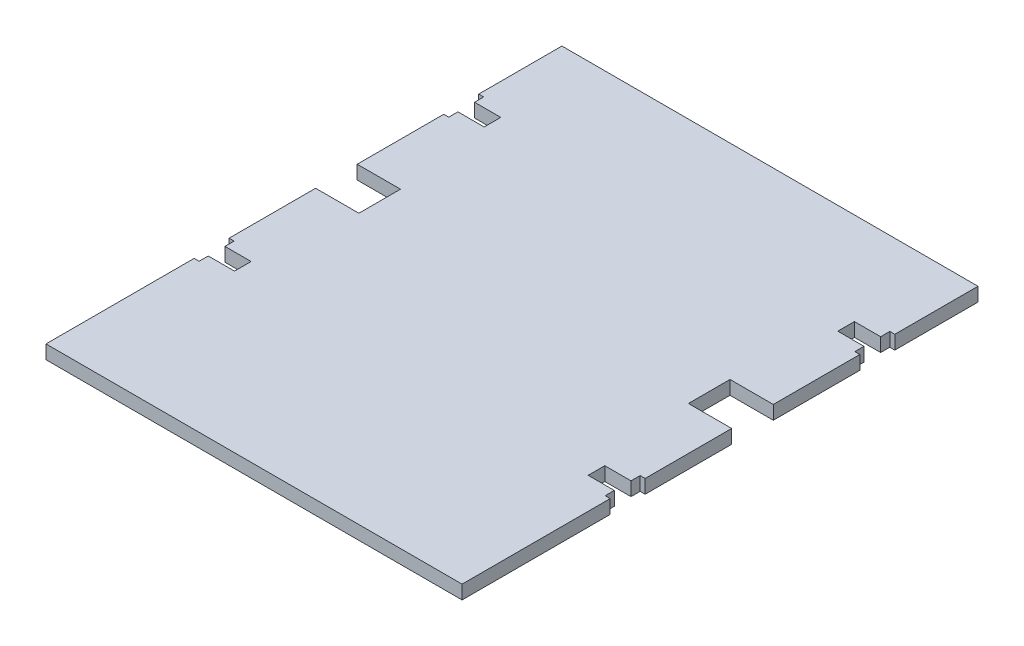
SolidWorks part; units mm, degrees
ref_plane "Front Plane" through (0, 0, 0) normal (0, 0, 1) x (1, 0, 0)
ref_plane "Top Plane" through (0, 0, 0) normal (0, 1, 0) x (1, 0, 0)
ref_plane "Right Plane" through (0, 0, 0) normal (1, 0, 0) x (0, 0, -1)
sketch "Sketch1" plane through (0, 0, 0) normal (0, 1, 0) x (1, 0, 0)
  line L1 (-250, -310) -> (250, -310)
  line L2 (-250, -310) -> (-250, 310)
  line L3 (-250, 310) -> (250, 310)
  line L4 (250, -310) -> (250, 310)
  line L5 (-250, -310) -> (250, 310) construction
  line L6 (-250, 310) -> (250, -310) construction
  point P0 (0, 0)
  dimension "D1" = 500
  dimension "D2" = 620
extrude "Boss-Extrude1" add sketch "Sketch1" along normal blind 16.5
sketch "Sketch2" plane through (0, 16.5, 0) normal (0, 1, 0) x (1, 0, 0)
  line L0 (-250, 310) -> (-250, -310) construction
  line L1 (-250, 64) -> (-198, 64)
  line L2 (-250, 64) -> (-250, 14)
  line L3 (-250, 14) -> (-198, 14)
  line L4 (-198, 64) -> (-198, 14)
  line L5 (250, -310) -> (250, 310) construction
  line L6 (250, 64) -> (198, 64)
  line L7 (250, 64) -> (250, 14)
  line L8 (250, 14) -> (198, 14)
  line L9 (198, 64) -> (198, 14)
  line L10 (250, 310) -> (-250, 310) construction
  line L11 (0, 310) -> (0, -310) construction
  line L12 (-250, 210) -> (-244, 210)
  line L13 (-250, 210) -> (-250, 168)
  line L14 (-250, 168) -> (-244, 168)
  line L15 (-244, 210) -> (-244, 199)
  line L16 (-244, 199) -> (-212.5, 199)
  line L18 (-244, 179) -> (-212.5, 179)
  line L19 (-212.5, 199) -> (-212.5, 179)
  line L20 (-250, -310) -> (250, -310) construction
  line L21 (-92.6056, 0) -> (108.2015, 0) construction
  line L22 (212.5, 199) -> (212.5, 179)
  line L23 (244, 179) -> (212.5, 179)
  line L25 (244, 199) -> (212.5, 199)
  line L26 (244, 210) -> (244, 199)
  line L27 (250, 168) -> (244, 168)
  line L28 (250, 210) -> (250, 168)
  line L29 (250, 210) -> (244, 210)
  line L46 (212.5, -101) -> (212.5, -121)
  line L47 (-250, -90) -> (-244, -90)
  line L48 (-250, -90) -> (-250, -132)
  line L49 (-250, -132) -> (-244, -132)
  line L50 (-244, -90) -> (-244, -101)
  line L51 (-244, -101) -> (-212.5, -101)
  line L53 (-244, -121) -> (-212.5, -121)
  line L54 (-212.5, -101) -> (-212.5, -121)
  line L55 (244, -121) -> (212.5, -121)
  line L57 (244, -101) -> (212.5, -101)
  line L58 (244, -90) -> (244, -101)
  line L59 (250, -132) -> (244, -132)
  line L60 (250, -90) -> (250, -132)
  line L61 (250, -90) -> (244, -90)
  line L62 (-244, 179) -> (-244, 168)
  line L63 (244, 179) -> (244, 168)
  line L64 (244, -121) -> (244, -132)
  line L65 (-244, -121) -> (-244, -132)
  dimension "D1" = 246
  dimension "D2" = 50
  dimension "D3" = 52
  dimension "D4" = 52
  dimension "D5" = 50
  dimension "D6" = 246
  dimension "D7" = 100
  dimension "D8" = 42
  dimension "D9" = 6
  dimension "D10" = 31.5
  dimension "D11" = 20
  dimension "D12" = 6
  dimension "D13" = 42
  dimension "D14" = 31.5
  dimension "D15" = 20
  dimension "D16" = 178
extrude "Cut-Extrude1" cut sketch "Sketch2" against normal through all
